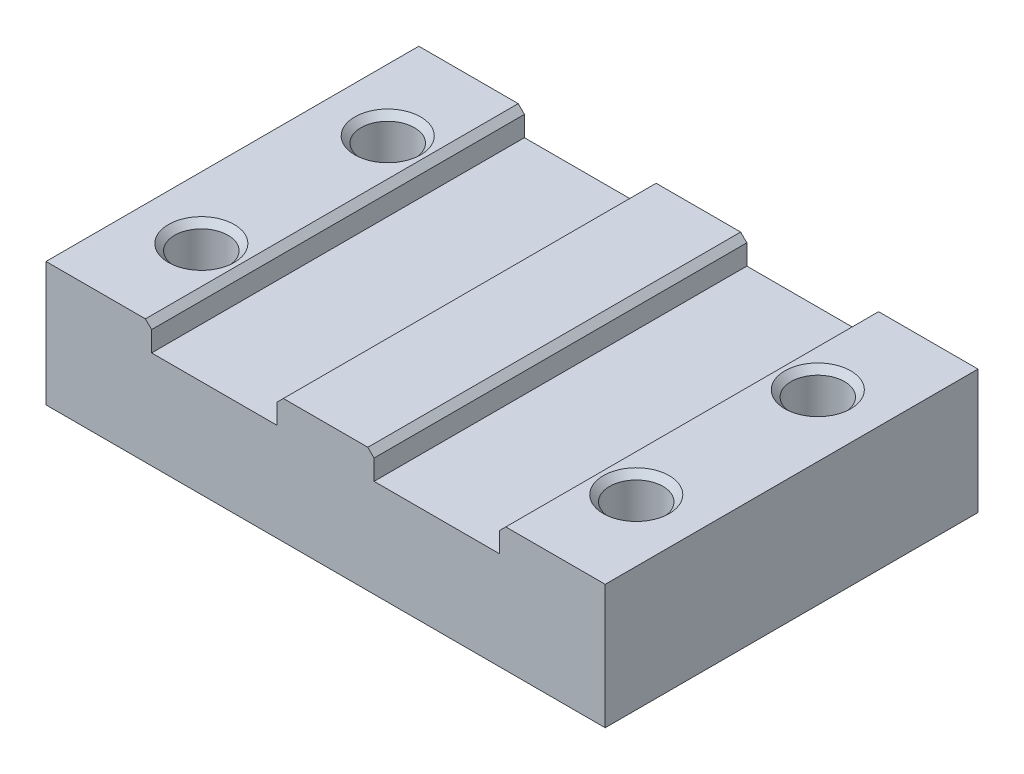
SolidWorks part; units mm, degrees
ref_plane "Спереди" through (0, 0, 0) normal (0, 0, 1) x (1, 0, 0)
ref_plane "Сверху" through (0, 0, 0) normal (0, 1, 0) x (1, 0, 0)
ref_plane "Справа" through (0, 0, 0) normal (1, 0, 0) x (0, 0, -1)
sketch "Sketch1" plane through (0, 0, 0) normal (0, 1, 0) x (1, 0, 0)
  line L1 (45, -30) -> (-45, -30)
  line L2 (45, -30) -> (45, 30)
  line L3 (45, 30) -> (-45, 30)
  line L4 (-45, -30) -> (-45, 30)
  line L5 (45, -30) -> (-45, 30) construction
  line L6 (45, 30) -> (-45, -30) construction
  point P0 (0, 0)
  dimension "D1" = 90
  dimension "D2" = 60
extrude "Boss-Extrude1" add sketch "Sketch1" along normal blind 20
sketch "Sketch2" plane through (0, 0, 30) normal (0, 0, 1) x (1, 0, 0)
  line L0 (-45, 20) -> (45, 20) construction
  line L1 (28, 24.25) -> (-28, 24.25)
  line L2 (28, 24.25) -> (28, 15.75)
  line L3 (28, 15.75) -> (-28, 15.75) construction
  line L4 (-28, 24.25) -> (-28, 15.75)
  line L5 (28, 24.25) -> (-28, 15.75) construction
  line L6 (28, 15.75) -> (-28, 24.25) construction
  line L7 (28, 15.75) -> (7.8, 15.75)
  line L8 (7.8, 15.75) -> (7.8, 20)
  line L9 (7.8, 20) -> (-7.8, 20)
  line L10 (-7.8, 20) -> (-7.8, 15.75)
  line L11 (-7.8, 15.75) -> (-28, 15.75)
  point P0 (0, 20)
  dimension "D1" = 56
  dimension "D2" = 8.5
  dimension "D3" = 20.2
extrude "Cut-Extrude1" cut sketch "Sketch2" against normal through all
sketch "Sketch3" plane through (0, 0, 0) normal (0, -1, 0) x (1, 0, 0)
  line L1 (-35, -15) -> (35, -15) construction
  line L2 (-35, -15) -> (-35, 15) construction
  line L3 (-35, 15) -> (35, 15) construction
  line L4 (35, -15) -> (35, 15) construction
  line L5 (-35, -15) -> (35, 15) construction
  line L6 (-35, 15) -> (35, -15) construction
  circle A0 centre (-35, 15) radius 4.3
  circle A1 centre (-35, -15) radius 4.3
  circle A2 centre (35, -14.2173) radius 4.3
  circle A3 centre (35, 15) radius 4.3
  point P0 (0, 0)
  dimension "D3" = 8.6
  dimension "D1" = 30
  dimension "D2" = 70
extrude "Cut-Extrude2" cut sketch "Sketch3" against normal through all
chamfer "Chamfer1" distance 1 angle 45 4 edges at (-28, 20, 0) (28, 20, 0) (-7.8, 20, 0) (7.8, 20, 0)
chamfer "Chamfer2" distance 1 angle 45 4 edges at (35, 20, -18.5173) (35, 20, 10.7) (-35, 20, 10.7) (-35, 20, -19.3)
